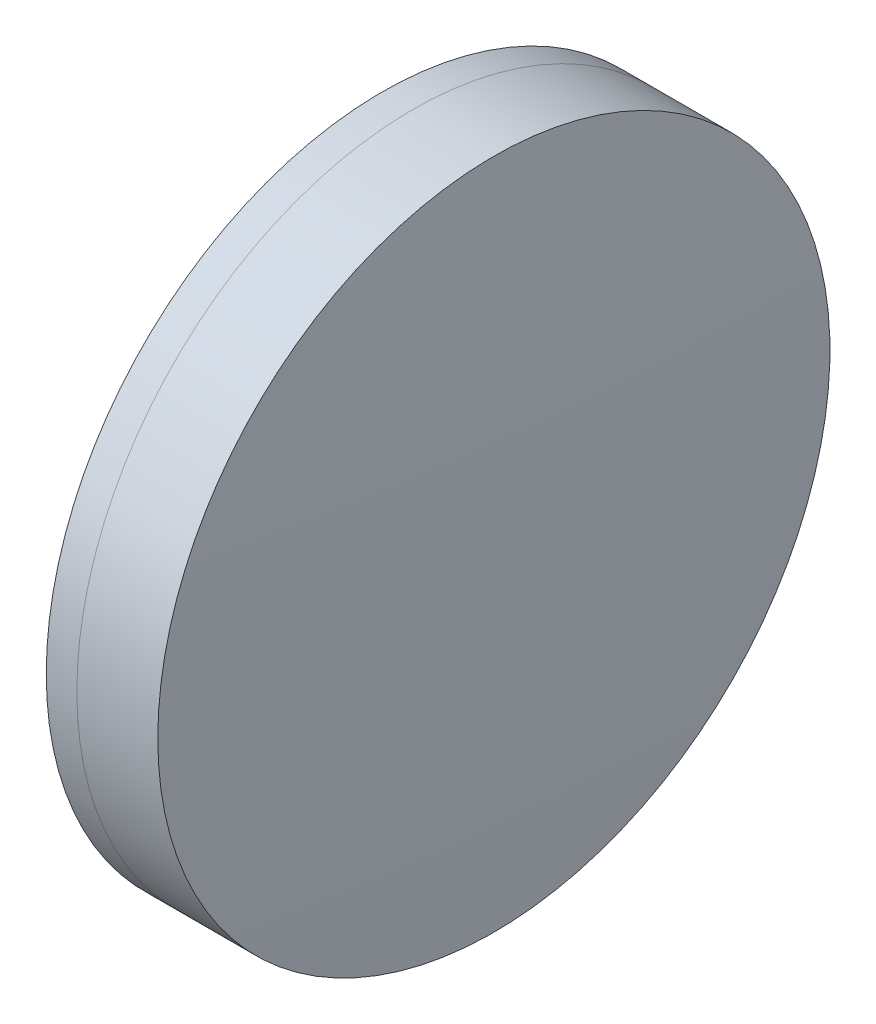
SolidWorks part; units mm, degrees
ref_plane "前视基准面" through (0, 0, 0) normal (0, 0, 1) x (1, 0, 0)
ref_plane "上视基准面" through (0, 0, 0) normal (0, 1, 0) x (1, 0, 0)
ref_plane "右视基准面" through (0, 0, 0) normal (1, 0, 0) x (0, 0, -1)
sketch "草图1" plane through (0, 0, 0) normal (0, 1, 0) x (1, 0, 0)
  line L0 (124.5233, 0) -> (395.1269, 0) construction
  line L1 (234.5265, -15) -> (235.8914, -15)
  line L2 (234.5265, 15) -> (235.8914, 15)
  arc A0 (235.8914, -15) -> (235.8914, 15) centre (180.9005, 0) ccw
  arc A1 (234.5265, 15) -> (234.5265, -15) centre (302.9005, 0) ccw
  point P10 (232.9005, 0)
  point P11 (237.9005, 0)
  dimension "D3" = 70
  dimension "D4" = 57
  dimension "D1" = 15
  dimension "D2" = 15
  dimension "D5" = 5
revolve "旋转1" add sketch "草图1" angle 360 about L0
sketch "草图2" plane through (0, 0, 0) normal (0, 1, 0) x (1, 0, 0)
  line L0 (-0.5519, 0) -> (409.4962, 0) construction
  line L2 (235.8914, 15) -> (239.5047, 15)
  line L3 (235.8914, -15) -> (239.5047, -15)
  arc A0 (239.5047, -15) -> (239.5047, 15) centre (-44.4995, 0) ccw
  arc A1 (235.8914, -15) -> (235.8914, 15) centre (180.9005, 0) ccw construction
  arc A2 (235.8914, -15) -> (235.8914, 15) centre (180.9005, 0) ccw
  point P4 (237.9005, 0)
  point P8 (239.9005, 0)
  dimension "D1" = 284.4
  dimension "D2" = 2
revolve "旋转3" add sketch "草图2" angle 360 about L0
